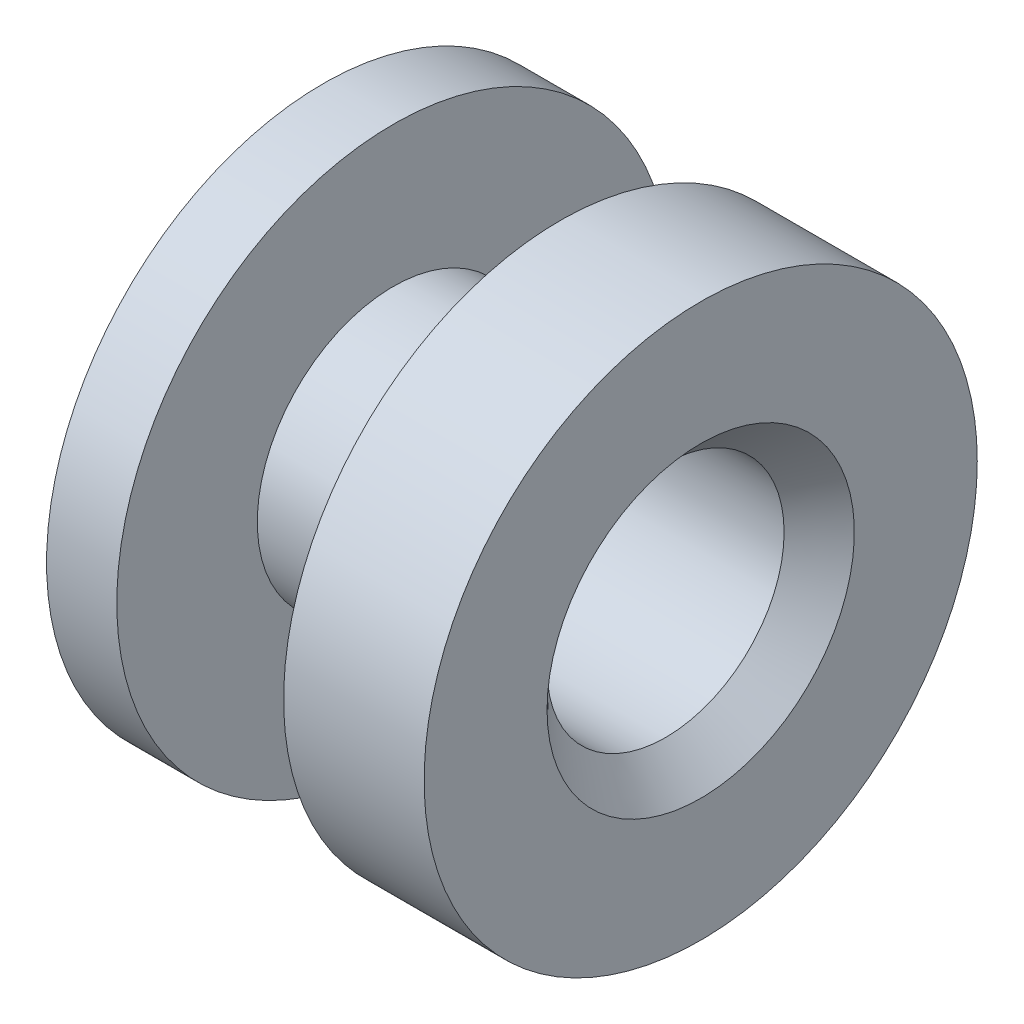
SolidWorks part; units mm, degrees
ref_plane "Front Plane" through (0, 0, 0) normal (0, 0, 1) x (1, 0, 0)
ref_plane "Top Plane" through (0, 0, 0) normal (0, 1, 0) x (1, 0, 0)
ref_plane "Right Plane" through (0, 0, 0) normal (1, 0, 0) x (0, 0, -1)
sketch "Sketch2" plane through (0, 0, 0) normal (0, 0, 1) x (1, 0, 0)
  line L0 (0, 0) -> (0, 8.001)
  line L1 (0, 0) -> (0, 7.874)
  line L2 (0, 8.001) -> (2.032, 8.001)
  line L3 (2.032, 8.001) -> (2.032, 3.937)
  line L4 (2.032, 3.937) -> (6.858, 3.937)
  line L5 (6.858, 3.937) -> (6.858, 8.001)
  line L6 (6.858, 8.001) -> (10.922, 8.001)
  line L7 (10.922, 8.001) -> (10.922, 0)
  line L8 (10.922, 0) -> (0, 0)
revolve "Revolve1" add sketch "Sketch2" angle 360 about L8
sketch "Sketch3" plane through (10.922, 0, 0) normal (1, 0, 0) x (0, 0, -1)
  circle A0 centre (0, 0) radius 3.429
extrude "Cut-Extrude1" cut sketch "Sketch3" against normal through all both
chamfer "Chamfer1" distance 1.016 angle 45 1 edges at (10.922, 0, -3.429)
